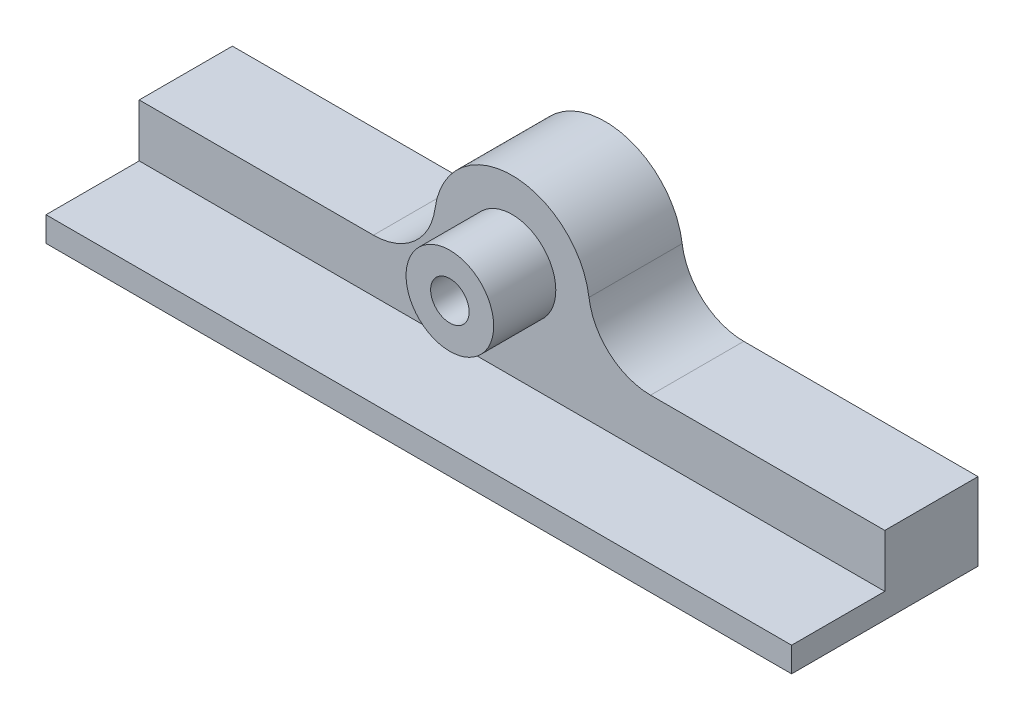
SolidWorks part; units mm, degrees
ref_plane "Front Plane" through (0, 0, 0) normal (0, 0, 1) x (1, 0, 0)
ref_plane "Top Plane" through (0, 0, 0) normal (0, 1, 0) x (1, 0, 0)
ref_plane "Right Plane" through (0, 0, 0) normal (1, 0, 0) x (0, 0, -1)
sketch "Sketch1" plane through (0, 0, 0) normal (0, 0, 1) x (1, 0, 0)
  line L2 (-2.4718, 1.7) -> (2.4718, 1.7)
  line L3 (-4.0792, 5.75) -> (4.0792, 5.75)
  arc A0 (-2.4718, 1.7) -> (2.4718, 1.7) centre (0, 0) ccw
  arc A2 (-4.0792, 5.75) -> (4.0792, 5.75) centre (0, 0) ccw
  arc A4 (-4.0792, 5.75) -> (4.0792, 5.75) centre (0, 0) cw
  arc A5 (-2.4718, 1.7) -> (2.4718, 1.7) centre (0, 0) cw
  arc A6 (-2.5542, 1.7567) -> (2.5542, 1.7567) centre (0, 0) cw
  arc A7 (-2.5542, 1.7567) -> (2.5542, 1.7567) centre (0, 0) ccw
  dimension "D1" = 6
  dimension "D2" = 1.7
  dimension "D3" = 0.1
extrude "Boss-Extrude1" add sketch "Sketch1" along normal blind 10 contours A4 L3 | L3 A2 A7 A6
sketch "Sketch2" plane through (0, 0, 0) normal (0, 0, -1) x (-1, 0, 0)
  line L0 (0, 7.05) -> (0, -7.05) construction
  line L5 (-60, 0) -> (60, 0) construction
  line L6 (0, 0) -> (0, -19.5) construction
  line L7 (0, -19.5) -> (-60, -19.5)
  line L8 (0, -19.5) -> (60, -19.5)
  line L9 (-60, -19.5) -> (-60, -7)
  line L10 (-60, -7) -> (-12.5, -7)
  line L11 (-12.5, 0) -> (-12.5, -7)
  line L12 (12.5, 0) -> (12.5, -7)
  line L13 (60, -19.5) -> (60, -7)
  line L14 (60, -7) -> (12.5, -7)
  circle A1 centre (0, 0) radius 12.5
  point P9 (0, 0)
  dimension "D1" = 25
  dimension "D2" = 19.5
  dimension "D3" = 12.5
extrude "Boss-Extrude2" add sketch "Sketch2" along normal blind 15 from surface
fillet "Fillet1" radius 10 2 edges at (-12.5, -7, -7.5) (12.5, -7, -7.5)
sketch "Sketch3" plane through (0, 0, 0) normal (0, 0, 1) x (1, 0, 0)
  line L0 (60, -19.5) -> (60, -7) construction
  line L1 (-60, -19.5) -> (60, -19.5)
  line L2 (-60, -19.5) -> (-60, -15.5)
  line L3 (-60, -15.5) -> (60, -15.5)
  line L4 (60, -19.5) -> (60, -15.5)
  dimension "D1" = 4
extrude "Boss-Extrude3" add sketch "Sketch3" along normal blind 15
